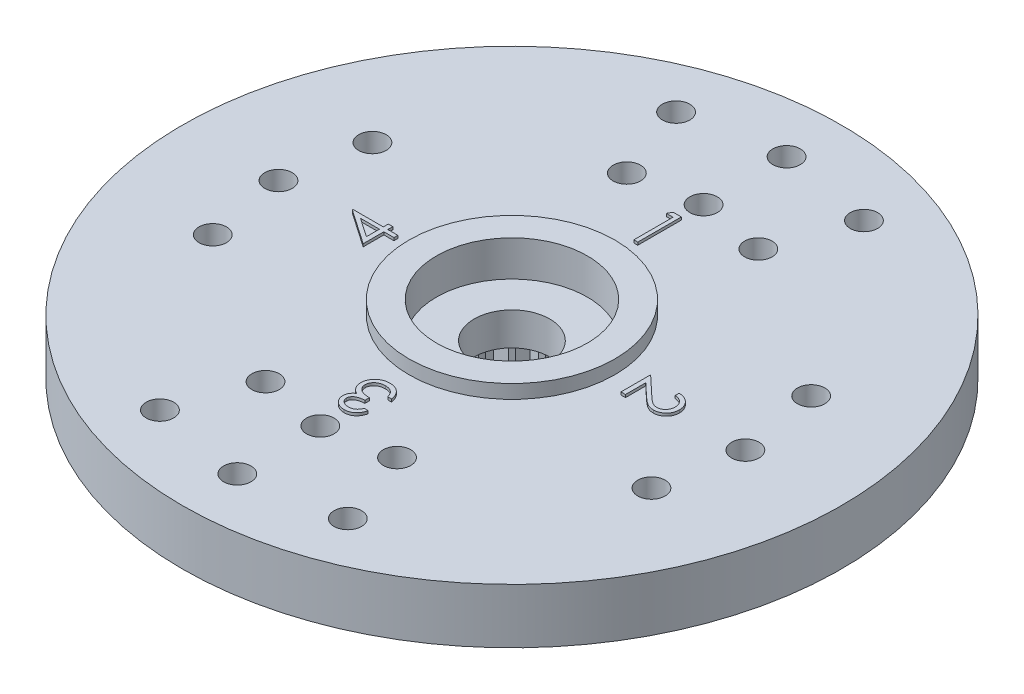
SolidWorks part; units mm, degrees
ref_plane "Front Plane" through (0, 0, 0) normal (0, 0, 1) x (1, 0, 0)
ref_plane "Top Plane" through (0, 0, 0) normal (0, 1, 0) x (1, 0, 0)
ref_plane "Right Plane" through (0, 0, 0) normal (1, 0, 0) x (0, 0, -1)
sketch "Sketch1" plane through (0, 0, 0) normal (0, 1, 0) x (1, 0, 0)
  line L0 (0, 12) -> (0, -12) construction
  line L1 (-12, 0) -> (12, 0) construction
  line L2 (0, 0) -> (3.4202, 9.3969) construction
  line L3 (-3.4202, 9.3969) -> (0, 0) construction
  line L4 (0, 0) -> (7.9874, 2.9072) construction
  line L5 (0, 0) -> (7.9874, -2.9072) construction
  circle A0 centre (0, 0) radius 12
  circle A1 centre (0, 0) radius 1.375
  circle A2 centre (0, 0) radius 7 construction
  circle A3 centre (0, 0) radius 10 construction
  circle A4 centre (0, 0) radius 8.5 construction
  circle A5 centre (0, 10) radius 0.5
  circle A6 centre (-3.4202, 9.3969) radius 0.5
  circle A7 centre (3.4202, 9.3969) radius 0.5
  circle A8 centre (0, 6.9777) radius 0.5
  circle A9 centre (-2.3941, 6.5778) radius 0.5
  circle A10 centre (2.3941, 6.5778) radius 0.5
  circle A11 centre (8.5, 0) radius 0.5
  circle A12 centre (7.9874, 2.9072) radius 0.5
  circle A13 centre (7.9874, -2.9072) radius 0.5
  circle A14 centre (-2.3941, -6.5778) radius 0.5
  circle A15 centre (0, -6.9777) radius 0.5
  circle A16 centre (2.3941, -6.5778) radius 0.5
  circle A17 centre (3.4202, -9.3969) radius 0.5
  circle A18 centre (0, -10) radius 0.5
  circle A19 centre (-3.4202, -9.3969) radius 0.5
  circle A20 centre (-7.9874, -2.9072) radius 0.5
  circle A21 centre (-8.5, 0) radius 0.5
  circle A22 centre (-7.9874, 2.9072) radius 0.5
  dimension "D1" = 24
  dimension "D2" = 2.75
  dimension "D3" = 14
  dimension "D4" = 20
  dimension "D5" = 17
  dimension "D6" = 1
  dimension "D7" = 1
  dimension "D9" = 1
  dimension "D11" = 1
  dimension "D12" = 1
  dimension "D13" = 1
  dimension "D16" = 1
  dimension "D17" = 1
  dimension "D18" = 1
  dimension "D8" = 20
  dimension "D10" = 20
  dimension "D14" = 20
  dimension "D15" = 20
extrude "Boss-Extrude1" add sketch "Sketch1" along normal blind 2
sketch "Sketch2" plane through (0, 2, 0) normal (0, 1, 0) x (1, 0, 0)
  circle A0 centre (0, 0) radius 3.75
  circle A1 centre (0, 0) radius 2.75
  dimension "D1" = 7.5
  dimension "D2" = 1
extrude "Boss-Extrude2" add sketch "Sketch2" along normal blind 0.5
sketch "Sketch3" plane through (0, 2, 0) normal (0, 1, 0) x (1, 0, 0)
  circle A0 centre (0, 0) radius 1.375 construction
  circle A1 centre (0, 0) radius 2.75 construction
  circle A2 centre (0, 0) radius 1.375
  circle A3 centre (0, 0) radius 2.75
extrude "Cut-Extrude1" cut sketch "Sketch3" against normal blind 0.8
sketch "Sketch4" plane through (0, 0, 0) normal (0, -1, 0) x (1, 0, 0)
  circle A0 centre (0, 0) radius 4.5
  circle A1 centre (0, 0) radius 2.5
  dimension "D1" = 9
  dimension "D2" = 2
extrude "Boss-Extrude3" add sketch "Sketch4" along normal blind 2.5
sketch "Sketch5" plane through (0, -2.5, 0) normal (0, -1, 0) x (1, 0, 0)
  line L0 (0, 0) -> (0, 0.6245) construction
  line L1 (0, 3) -> (-0.299, 2.4821)
  line L2 (0, 3) -> (0.299, 2.4821)
  line L3 (0.9271, 2.8532) -> (0.4826, 2.453)
  line L4 (0.9271, 2.8532) -> (1.0514, 2.2682)
  line L5 (1.7634, 2.4271) -> (1.217, 2.1838)
  line L6 (1.7634, 2.4271) -> (1.7008, 1.8323)
  line L7 (2.4271, 1.7634) -> (1.8323, 1.7008)
  line L8 (2.4271, 1.7634) -> (2.1838, 1.217)
  line L9 (2.8532, 0.9271) -> (2.2682, 1.0514)
  line L10 (2.8532, 0.9271) -> (2.453, 0.4826)
  line L11 (3, 0) -> (2.4821, 0.299)
  line L12 (3, 0) -> (2.4821, -0.299)
  line L13 (2.8532, -0.9271) -> (2.453, -0.4826)
  line L14 (2.8532, -0.9271) -> (2.2682, -1.0514)
  line L15 (2.4271, -1.7634) -> (2.1838, -1.217)
  line L16 (2.4271, -1.7634) -> (1.8323, -1.7008)
  line L17 (1.7634, -2.4271) -> (1.7008, -1.8323)
  line L18 (1.7634, -2.4271) -> (1.217, -2.1838)
  line L19 (0.9271, -2.8532) -> (1.0514, -2.2682)
  line L20 (0.9271, -2.8532) -> (0.4826, -2.453)
  line L21 (0, -3) -> (0.299, -2.4821)
  line L22 (0, -3) -> (-0.299, -2.4821)
  line L23 (-0.9271, -2.8532) -> (-0.4826, -2.453)
  line L24 (-0.9271, -2.8532) -> (-1.0514, -2.2682)
  line L25 (-1.7634, -2.4271) -> (-1.217, -2.1838)
  line L26 (-1.7634, -2.4271) -> (-1.7008, -1.8323)
  line L27 (-2.4271, -1.7634) -> (-1.8323, -1.7008)
  line L28 (-2.4271, -1.7634) -> (-2.1838, -1.217)
  line L29 (-2.8532, -0.9271) -> (-2.2682, -1.0514)
  line L30 (-2.8532, -0.9271) -> (-2.453, -0.4826)
  line L31 (-3, 0) -> (-2.4821, -0.299)
  line L32 (-3, 0) -> (-2.4821, 0.299)
  line L33 (-2.8532, 0.9271) -> (-2.453, 0.4826)
  line L34 (-2.8532, 0.9271) -> (-2.2682, 1.0514)
  line L35 (-2.4271, 1.7634) -> (-2.1838, 1.217)
  line L36 (-2.4271, 1.7634) -> (-1.8323, 1.7008)
  line L37 (-1.7634, 2.4271) -> (-1.7008, 1.8323)
  line L38 (-1.7634, 2.4271) -> (-1.217, 2.1838)
  line L39 (-0.9271, 2.8532) -> (-1.0514, 2.2682)
  line L40 (-0.9271, 2.8532) -> (-0.4826, 2.453)
  circle A0 centre (0, 0) radius 2.5 construction
  arc A1 (-2.1838, 1.217) -> (-2.2682, 1.0514) centre (0, 0) ccw
  arc A2 (-1.7008, 1.8323) -> (-1.8323, 1.7008) centre (0, 0) ccw
  arc A3 (-1.0514, 2.2682) -> (-1.217, 2.1838) centre (0, 0) ccw
  arc A4 (-0.299, 2.4821) -> (-0.4826, 2.453) centre (0, 0) ccw
  arc A5 (0.4826, 2.453) -> (0.299, 2.4821) centre (0, 0) ccw
  arc A6 (1.217, 2.1838) -> (1.0514, 2.2682) centre (0, 0) ccw
  arc A7 (1.8323, 1.7008) -> (1.7008, 1.8323) centre (0, 0) ccw
  arc A8 (2.2682, 1.0514) -> (2.1838, 1.217) centre (0, 0) ccw
  arc A9 (2.4821, 0.299) -> (2.453, 0.4826) centre (0, 0) ccw
  arc A10 (2.453, -0.4826) -> (2.4821, -0.299) centre (0, 0) ccw
  arc A11 (2.1838, -1.217) -> (2.2682, -1.0514) centre (0, 0) ccw
  arc A12 (1.7008, -1.8323) -> (1.8323, -1.7008) centre (0, 0) ccw
  arc A13 (1.0514, -2.2682) -> (1.217, -2.1838) centre (0, 0) ccw
  arc A14 (0.299, -2.4821) -> (0.4826, -2.453) centre (0, 0) ccw
  arc A15 (-0.4826, -2.453) -> (0, -2.5) centre (0, 0) ccw
  arc A16 (-1.217, -2.1838) -> (-1.0514, -2.2682) centre (0, 0) ccw
  arc A17 (-1.8323, -1.7008) -> (-1.7008, -1.8323) centre (0, 0) ccw
  arc A18 (-2.2682, -1.0514) -> (-2.1838, -1.217) centre (0, 0) ccw
  arc A19 (-2.4821, -0.299) -> (-2.453, -0.4826) centre (0, 0) ccw
  arc A20 (-2.453, 0.4826) -> (-2.4821, 0.299) centre (0, 0) ccw
  point P68 (0, 0)
  circle M5 centre (0, 0) radius 2.5
  dimension "D1" = 30
  dimension "D2" = 3
  dimension "D3" = 20
extrude "Cut-Extrude3" cut sketch "Sketch5" against normal up to surface (2.5 mm away) contours L36 L35 M5 | L34 L33 M5 | L32 L31 M5 | L30 L29 M5 | L28 L27 M5 | L26 L25 M5 | L24 L23 M5 | L0 L21 M5 | L22 L0 M5 | L20 L19 M5 | L18 L17 M5 | L16 L15 M5 | L14 L13 M5 | L12 L11 M5 | L10 L9 M5 | L8 L7 M5 | L6 L5 M5 | L4 L3 M5 | L0 L2 M5 | L0 L1 M5 | L40 L39 M5 | L38 L37 M5
sketch "Sketch6" plane through (0, 2, 0) normal (0, 1, 0) x (1, 0, 0)
  line L1 (4.5, -4.5) -> (-4.5, -4.5) construction
  line L2 (4.5, -4.5) -> (4.5, 4.5) construction
  line L3 (4.5, 4.5) -> (-4.5, 4.5) construction
  line L4 (-4.5, -4.5) -> (-4.5, 4.5) construction
  line L5 (4.5, -4.5) -> (-4.5, 4.5) construction
  line L6 (4.5, 4.5) -> (-4.5, -4.5) construction
  circle A0 centre (0, 0) radius 4.5 construction
  text T0 "1" font "Century Gothic" height in points 6
  text T1 "2" font "Century Gothic" height in points 6
  text T2 "3" font "Century Gothic" height in points 6
  text T3 "4" font "Century Gothic" height in points 6
  dimension "D1" = 9
  dimension "D2" = 9
  dimension "D3" = 9
extrude "Boss-Extrude4" add sketch "Sketch6" along normal blind 0.1
